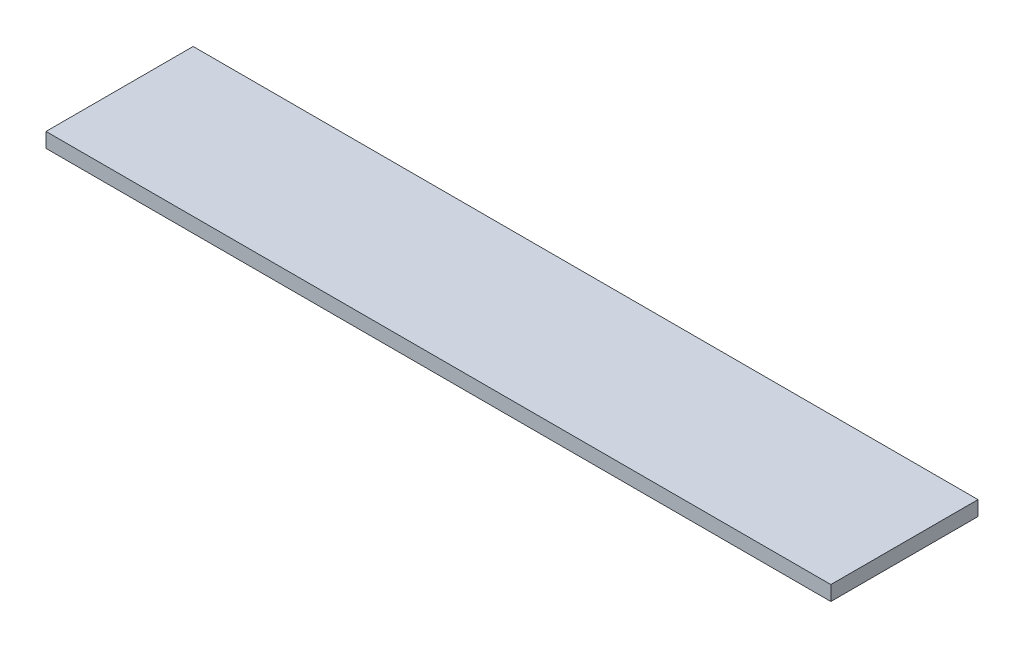
SolidWorks part; units mm, degrees
ref_plane "Front Plane" through (0, 0, 0) normal (0, 0, 1) x (1, 0, 0)
ref_plane "Top Plane" through (0, 0, 0) normal (0, 1, 0) x (1, 0, 0)
ref_plane "Right Plane" through (0, 0, 0) normal (1, 0, 0) x (0, 0, -1)
sketch "Sketch1" plane through (0, 0, 0) normal (0, 1, 0) x (1, 0, 0)
  line L1 (0, 0) -> (10.16, 0)
  line L2 (0, 0) -> (0, 1.905)
  line L3 (0, 1.905) -> (10.16, 1.905)
  line L4 (10.16, 0) -> (10.16, 1.905)
  dimension "D1" = 10.16
  dimension "D2" = 1.905
extrude "Boss-Extrude1" add sketch "Sketch1" along normal blind 0.1905
